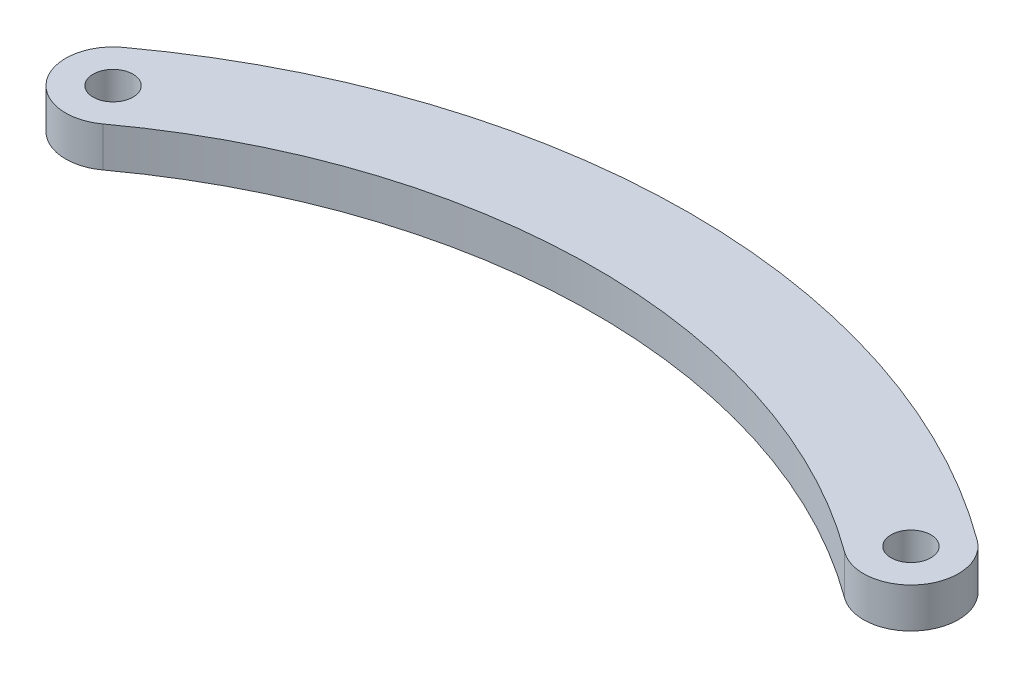
SolidWorks part; units mm, degrees
ref_plane "Front" through (0, 0, 0) normal (0, 0, 1) x (1, 0, 0)
ref_plane "Top" through (0, 0, 0) normal (0, 1, 0) x (1, 0, 0)
ref_plane "Right" through (0, 0, 0) normal (1, 0, 0) x (0, 0, -1)
sketch "Sketch2" plane through (0, 0, 0) normal (0, 1, 0) x (1, 0, 0)
  arc A0 (-29.3923, -2.2005) -> (34.1077, -2.2005) centre (2.3577, -45.5043) cw construction
  arc A1 (36.3398, 0.8439) -> (-31.6245, 0.8439) centre (2.3577, -45.5043) ccw
  arc A2 (31.8755, -5.2449) -> (-27.1602, -5.2449) centre (2.3577, -45.5043) ccw
  arc A3 (31.8755, -5.2449) -> (36.3398, 0.8439) centre (34.1077, -2.2005) ccw
  arc A4 (-31.6245, 0.8439) -> (-27.1602, -5.2449) centre (-29.3923, -2.2005) ccw
  point P0 (-29.3923, -2.2005)
  point P1 (34.1077, -2.2005)
  point P5 (2.3577, 8.1919)
  dimension "D1" = 63.5
extrude "Boss-Extrude1" add sketch "Sketch2" along normal blind 3.175
sketch "Sketch3" plane through (0, 3.175, 0) normal (0, 1, 0) x (1, 0, 0)
  circle A0 centre (-29.3923, -2.2005) radius 1.5875
  circle A1 centre (34.1077, -2.2005) radius 1.5875
  dimension "D1" = 3.175
  dimension "D2" = 3.175
extrude "Cut-Extrude1" cut sketch "Sketch3" against normal blind 3.175
